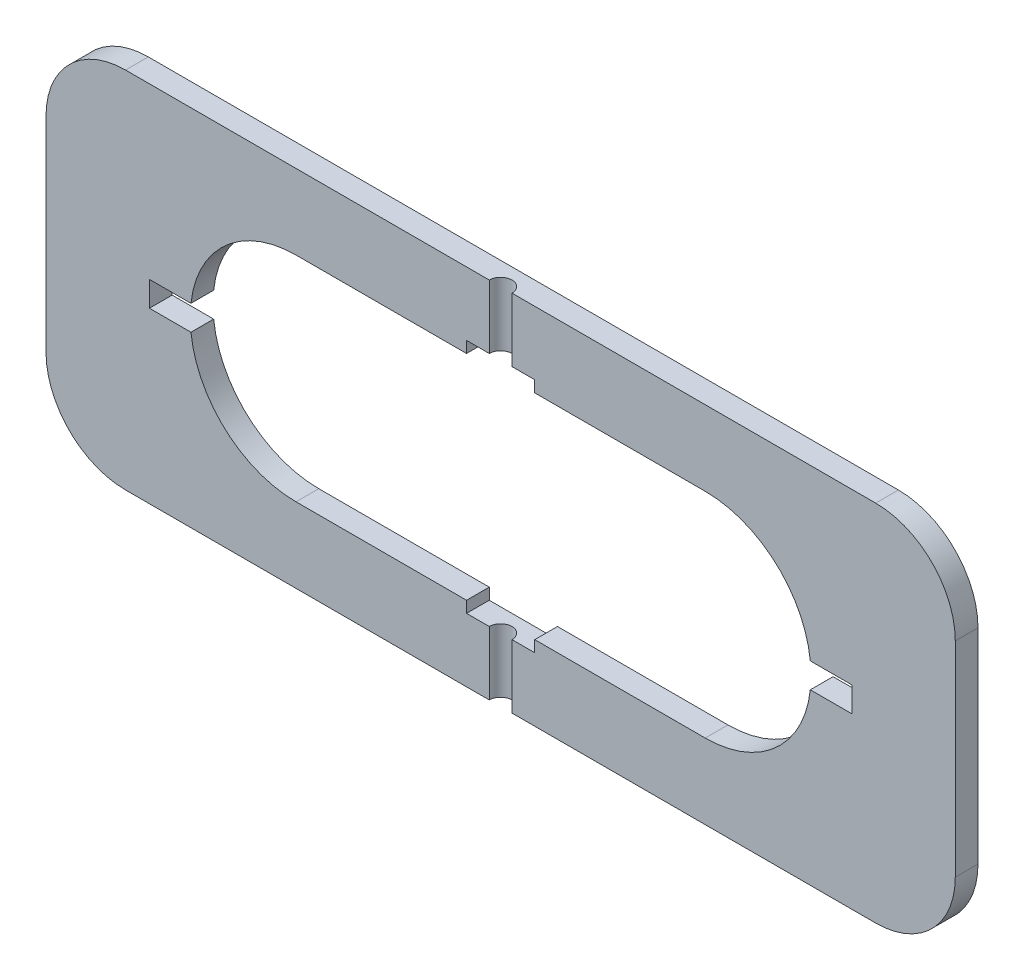
SolidWorks part; units mm, degrees
ref_plane "Plan de face" through (0, 0, 0) normal (0, 0, 1) x (1, 0, 0)
ref_plane "Plan de dessus" through (0, 0, 0) normal (0, 1, 0) x (1, 0, 0)
ref_plane "Plan de droite" through (0, 0, 0) normal (1, 0, 0) x (0, 0, -1)
sketch "Esquisse2" plane through (0, 0, 0) normal (0, 0, 1) x (1, 0, 0)
  line L1 (165, 80) -> (-165, 80)
  line L2 (200, 45) -> (200, -45)
  line L3 (165, -80) -> (-165, -80)
  line L4 (-200, 45) -> (-200, -45)
  line L5 (200, 80) -> (-200, -80) construction
  line L6 (200, -80) -> (-200, 80) construction
  arc A0 (165, 80) -> (200, 45) centre (165, 45) cw
  arc A1 (200, -45) -> (165, -80) centre (165, -45) cw
  arc A2 (-165, -80) -> (-200, -45) centre (-165, -45) cw
  arc A3 (-165, 80) -> (-200, 45) centre (-165, 45) ccw
  point P0 (0, 0)
  dimension "D3" = 35
  dimension "D1" = 160
  dimension "D2" = 400
extrude "Boss.-Extru.2" add sketch "Esquisse2" along normal blind 10
sketch "Esquisse3" plane through (0, 0, 10) normal (0, 0, 1) x (1, 0, 0)
  line L1 (90, 47) -> (-90, 47)
  line L2 (136.5, 0.5) -> (136.5, -0.5)
  line L3 (90, -47) -> (-90, -47)
  line L4 (-136.5, 0.5) -> (-136.5, -0.5)
  line L5 (136.5, 47) -> (-136.5, -47) construction
  line L6 (136.5, -47) -> (-136.5, 47) construction
  arc A0 (136.5, -0.5) -> (90, -47) centre (90, -0.5) cw
  arc A1 (90, 47) -> (136.5, 0.5) centre (90, 0.5) cw
  arc A2 (-90, -47) -> (-136.5, -0.5) centre (-90, -0.5) cw
  arc A3 (-90, 47) -> (-136.5, 0.5) centre (-90, 0.5) ccw
  point P0 (0, 0)
  dimension "D3" = 46.5
  dimension "D1" = 94
  dimension "D2" = 273
extrude "Enlèv. mat.-Extru.1" cut sketch "Esquisse3" against normal blind 10
sketch "Esquisse4" plane through (0, 0, 10) normal (0, 0, 1) x (1, 0, 0)
  line L0 (-136.5, 0.5) -> (-136.5, -0.5) construction
  line L1 (154.5, -5.5) -> (-154.5, -5.5)
  line L2 (154.5, -5.5) -> (154.5, 5.5)
  line L3 (154.5, 5.5) -> (-154.5, 5.5)
  line L4 (-154.5, -5.5) -> (-154.5, 5.5)
  line L5 (154.5, -5.5) -> (-154.5, 5.5) construction
  line L6 (154.5, 5.5) -> (-154.5, -5.5) construction
  point P0 (0, 0)
  dimension "D1" = 11
  dimension "D2" = 18
extrude "Enlèv. mat.-Extru.2" cut sketch "Esquisse4" against normal blind 10
sketch "Esquisse5" plane through (0, 0, 10) normal (0, 0, 1) x (1, 0, 0)
  line L0 (90, 47) -> (-90, 47) construction
  line L1 (15, -52) -> (-15, -52)
  line L2 (15, -52) -> (15, 52)
  line L3 (15, 52) -> (-15, 52)
  line L4 (-15, -52) -> (-15, 52)
  line L5 (15, -52) -> (-15, 52) construction
  line L6 (15, 52) -> (-15, -52) construction
  point P0 (0, 0)
  dimension "D1" = 30
  dimension "D2" = 5
extrude "Enlèv. mat.-Extru.3" cut sketch "Esquisse5" against normal blind 10
sketch "Esquisse6" plane through (0, -80, 0) normal (0, -1, 0) x (1, 0, 0)
  line L0 (-165, 10) -> (165, 10) construction
  circle A0 centre (0, 10) radius 5
extrude "Enlèv. mat.-Extru.4" cut sketch "Esquisse6" against normal through all
